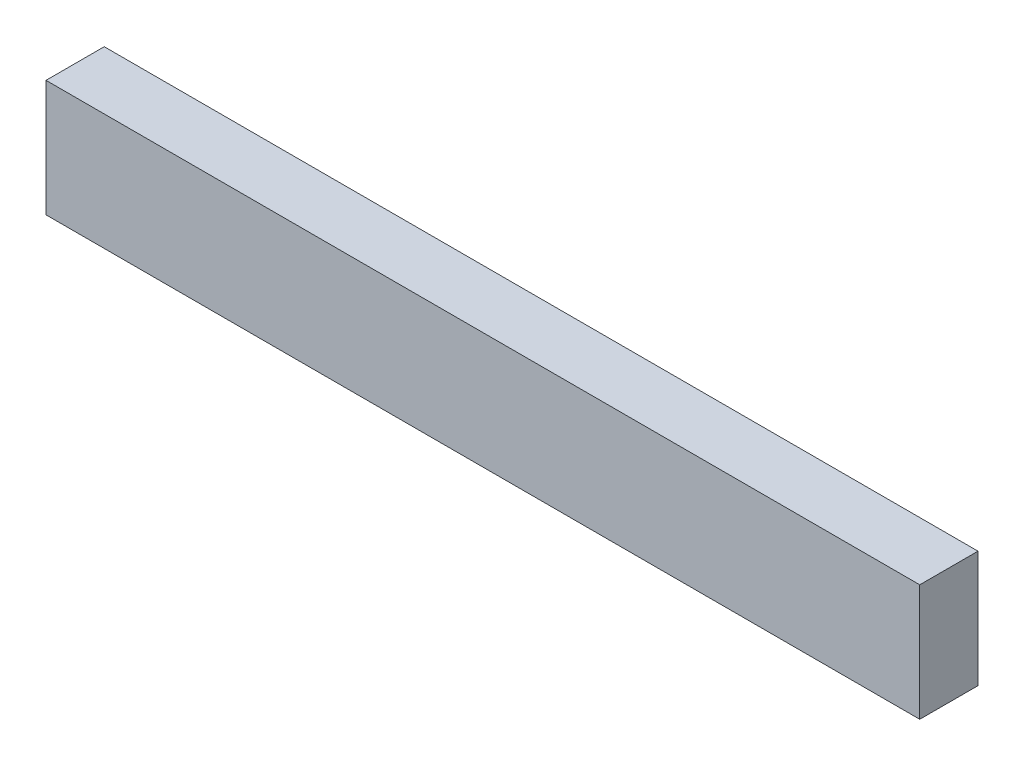
SolidWorks part; units mm, degrees
ref_plane "Front Plane" through (0, 0, 0) normal (0, 0, 1) x (1, 0, 0)
ref_plane "Top Plane" through (0, 0, 0) normal (0, 1, 0) x (1, 0, 0)
ref_plane "Right Plane" through (0, 0, 0) normal (1, 0, 0) x (0, 0, -1)
sketch "Sketch1" plane through (0, 0, 0) normal (0, 0, 1) x (1, 0, 0)
  line L1 (-75, -10) -> (75, -10)
  line L2 (-75, -10) -> (-75, 10)
  line L3 (-75, 10) -> (75, 10)
  line L4 (75, -10) -> (75, 10)
  line L5 (-75, -10) -> (75, 10) construction
  line L6 (-75, 10) -> (75, -10) construction
  point P0 (0, 0)
  dimension "D1" = 150
  dimension "D2" = 20
extrude "Boss-Extrude1" add sketch "Sketch1" along normal blind 10
